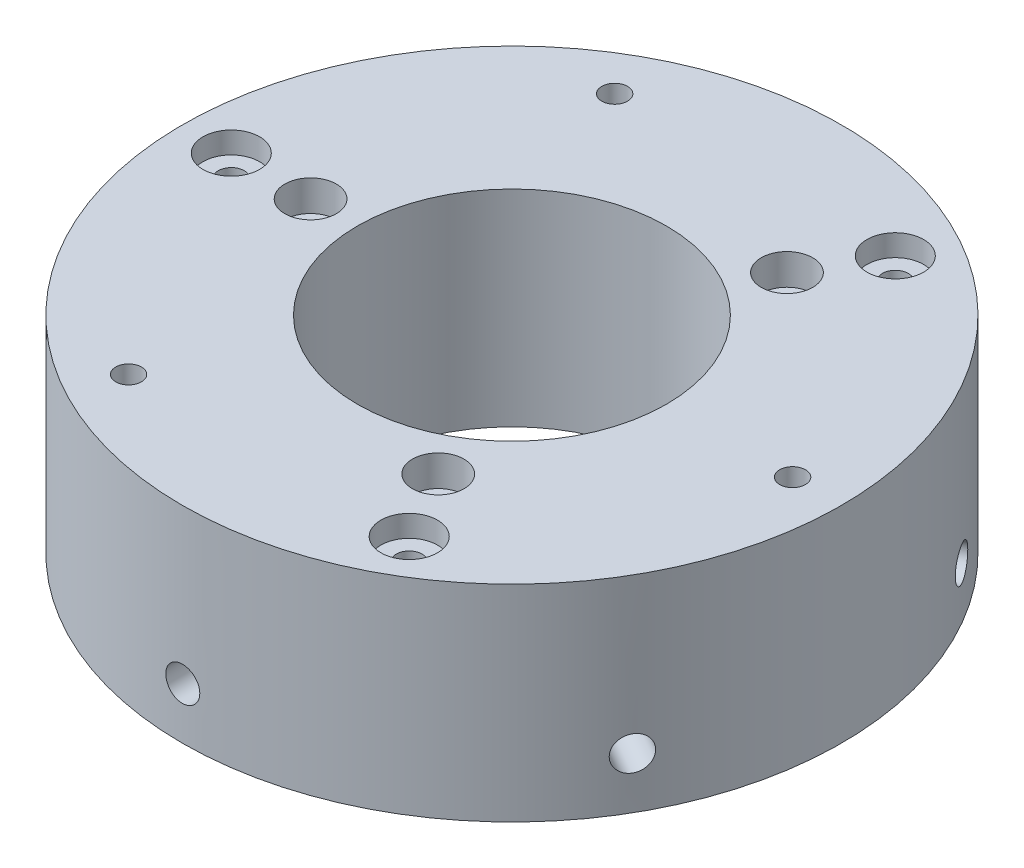
SolidWorks part; units mm, degrees
material "6061 合金"
ref_plane "前视基准面" through (0, 0, 0) normal (0, 0, 1) x (1, 0, 0)
ref_plane "上视基准面" through (0, 0, 0) normal (0, 1, 0) x (1, 0, 0)
ref_plane "右视基准面" through (0, 0, 0) normal (1, 0, 0) x (0, 0, -1)
sketch "草图1" plane through (0, 0, 0) normal (0, 1, 0) x (1, 0, 0)
  circle A0 centre (0, 0) radius 32
  circle A1 centre (0, 0) radius 27.25 construction
  circle A3 centre (-27.25, 0) radius 1.25
  circle A5 centre (-23.5992, 13.625) radius 2.5
  circle A6 centre (-13.625, 23.5992) radius 1.25
  circle A9 centre (0, 27.25) radius 2.5
  circle A10 centre (13.625, 23.5992) radius 1.25
  circle A13 centre (23.5992, 13.625) radius 2.5
  circle A14 centre (27.25, 0) radius 1.25
  circle A17 centre (23.5992, -13.625) radius 2.5
  circle A18 centre (13.625, -23.5992) radius 1.25
  circle A21 centre (0, -27.25) radius 2.5
  circle A22 centre (-13.625, -23.5992) radius 1.25
  circle A25 centre (-23.5992, -13.625) radius 2.5
  circle A26 centre (-23.5992, -13.625) radius 1.25 [skipped]
  circle A27 centre (-23.5992, 13.625) radius 1.25 [skipped]
  circle A28 centre (0, 27.25) radius 1.25 [skipped]
  circle A29 centre (23.5992, 13.625) radius 1.25 [skipped]
  circle A30 centre (23.5992, -13.625) radius 1.25 [skipped]
  circle A31 centre (0, -27.25) radius 1.25 [skipped]
  point P43 (0, 0)
  dimension "D1" = 12
extrude "凸台-拉伸1" add sketch "草图1" along normal blind 20 contours A0 A25 A22 A21 A18 A17 A14 A13 A10 A9 A6 A5 A3 | A25 | A5 | A13 | A9 | A21 | A17
sketch "草图2" plane through (0, 20, 0) normal (0, 1, 0) x (1, 0, 0)
  circle A0 centre (0, 0) radius 27.25 construction
  circle A1 centre (-27.25, 0) radius 2.75
  circle A2 centre (13.625, 23.5992) radius 2.75
  circle A3 centre (13.625, -23.5992) radius 2.75
  point P12 (0, 0)
  dimension "D1" = 3
extrude "切除-拉伸1" cut sketch "草图2" against normal blind 2.1
sketch "草图3" plane through (0, 20, 0) normal (0, 1, 0) x (1, 0, 0)
  circle A0 centre (0, 0) radius 19.55
  circle A1 centre (-19.55, 0) radius 2.5
  circle A2 centre (9.775, 16.9308) radius 2.5
  circle A3 centre (9.775, -16.9308) radius 2.5
  point P11 (0, 0)
  dimension "D1" = 3
extrude "切除-拉伸2" cut sketch "草图3" against normal blind 3 contours A0 A1 | A0 A1 | A0 A2 | A0 A2 | A0 A3 | A0 A3
ref_plane "基准面1" through (0, 0, 32) normal (0, 0, 1) x (1, 0, 0)
sketch "草图4" plane through (0, 0, 32) normal (0, 0, 1) x (1, 0, 0)
  circle A0 centre (0, 5) radius 1.65
extrude "切除-拉伸3" cut sketch "草图4" against normal blind 10 contours A0
pattern_circular "阵列(圆周)1" count 6 over 360 about axis through (0, 0, 0) along (0, 1, 0) of "切除-拉伸3"
sketch "草图5" plane through (0, 20, 0) normal (0, 1, 0) x (1, 0, 0)
  circle A0 centre (0, 0) radius 15
extrude "切除-拉伸4" cut sketch "草图5" against normal through all
sketch "草图6" plane through (0, 0, 0) normal (0, -1, 0) x (1, 0, 0)
  circle A0 centre (-13.625, 23.5992) radius 1.25 construction
  circle A1 centre (0, 0) radius 32
  circle A2 centre (0, 0) radius 32
  circle A3 centre (-13.625, 23.5992) radius 1.25
  circle A4 centre (13.625, 23.5992) radius 1.25 construction
  circle A5 centre (13.625, 23.5992) radius 1.25
  circle A6 centre (27.25, 0) radius 1.25 construction
  circle A7 centre (27.25, 0) radius 1.25
  circle A8 centre (13.625, -23.5992) radius 1.25 construction
  circle A9 centre (13.625, -23.5992) radius 1.25
  circle A10 centre (-13.625, -23.5992) radius 1.25 construction
  circle A11 centre (-13.625, -23.5992) radius 1.25
  circle A12 centre (-27.25, 0) radius 1.25 construction
  circle A13 centre (-27.25, 0) radius 1.25
  circle A14 centre (-27.25, 0) radius 2.75
  circle A15 centre (-13.625, 23.5992) radius 2.75
  circle A16 centre (13.625, 23.5992) radius 2.75
  circle A17 centre (27.25, 0) radius 2.75
  circle A18 centre (13.625, -23.5992) radius 2.75
  circle A19 centre (-13.625, -23.5992) radius 2.75
  point P34 (0, 0)
  circle M3 centre (-13.625, 23.5992) radius 1.25
  circle M4 centre (13.625, 23.5992) radius 1.25
  circle M5 centre (27.25, 0) radius 1.25
  circle M6 centre (13.625, -23.5992) radius 1.25
  circle M7 centre (-13.625, -23.5992) radius 1.25
  circle M8 centre (-27.25, 0) radius 1.25
  dimension "D2" = 6
  dimension "D1" = 0
extrude "切除-拉伸5" cut sketch "草图6" against normal blind 3 contours A18 M6 | A17 M5 | A16 M4 | A15 M3 | A14 M8 | A19 M7
